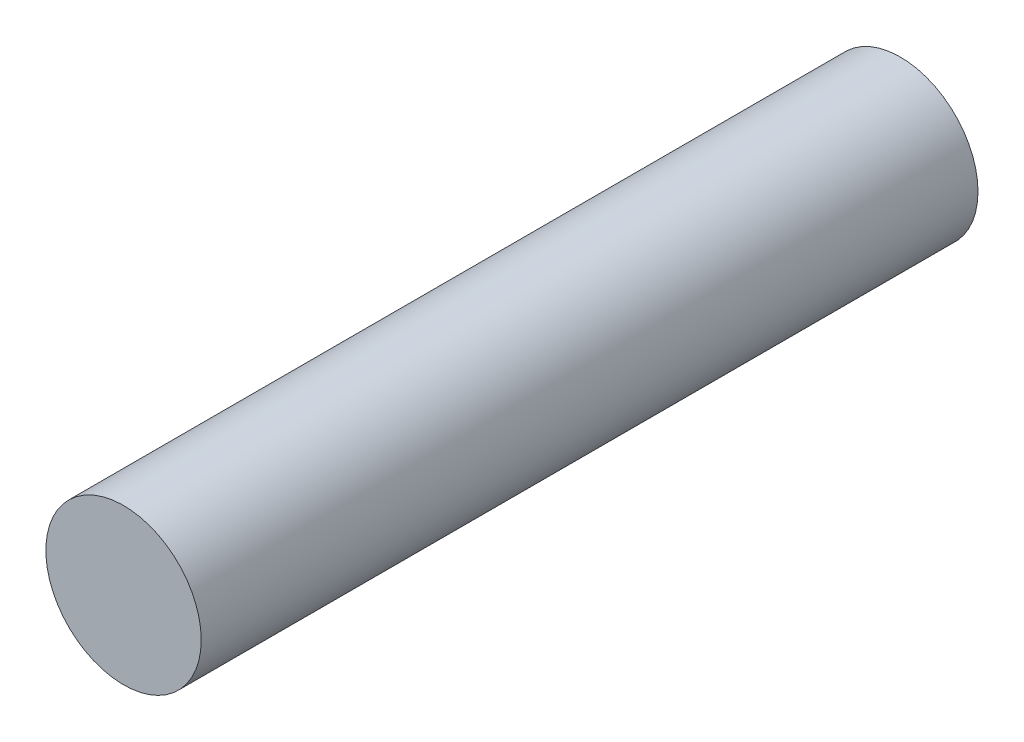
SolidWorks part; units mm, degrees
ref_plane "Ön Düzlem" through (0, 0, 0) normal (0, 0, 1) x (1, 0, 0)
ref_plane "Üst Düzlem" through (0, 0, 0) normal (0, 1, 0) x (1, 0, 0)
ref_plane "Sağ Düzlem" through (0, 0, 0) normal (1, 0, 0) x (0, 0, -1)
sketch "Sketch1" plane through (0, 0, 0) normal (0, 0, 1) x (1, 0, 0)
  circle A0 centre (-16.0296, 18.9228) radius 3.5
extrude "Boss-Extrude1" add sketch "Sketch1" along normal blind 35
